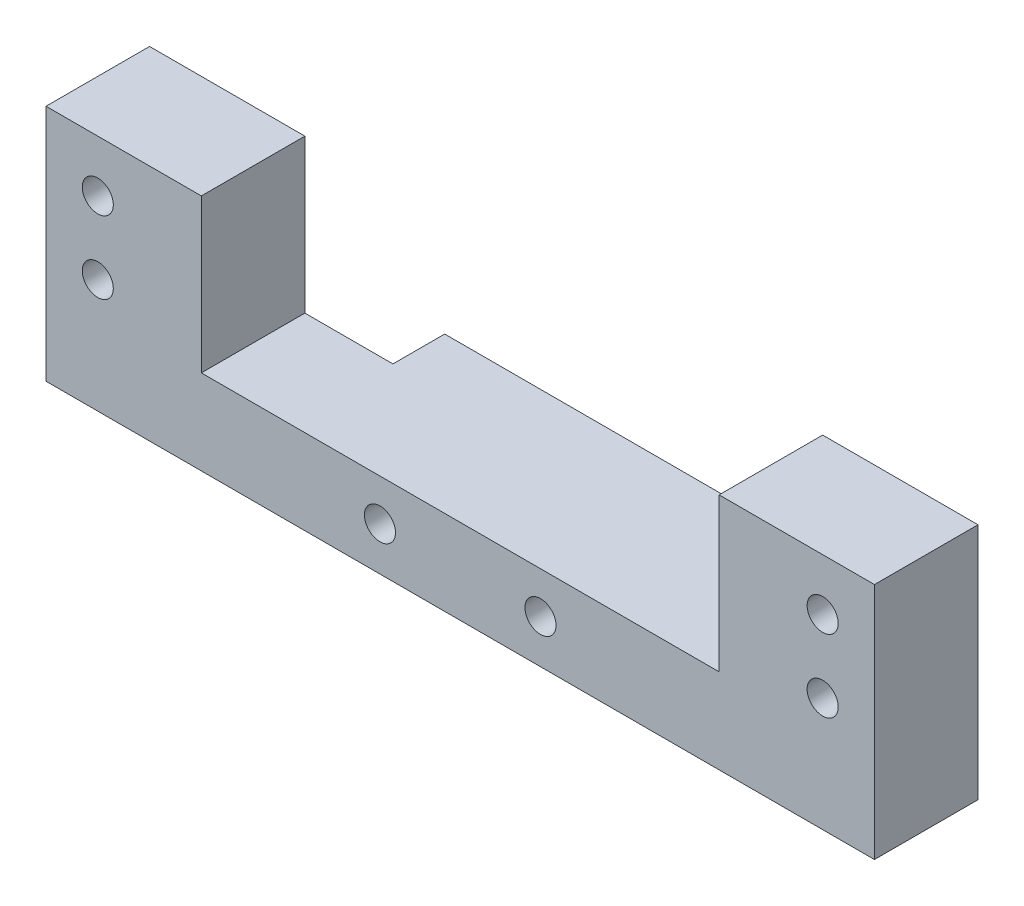
SolidWorks part; units mm, degrees
ref_plane "Front Plane" through (0, 0, 0) normal (0, 0, 1) x (1, 0, 0)
ref_plane "Top Plane" through (0, 0, 0) normal (0, 1, 0) x (1, 0, 0)
ref_plane "Right Plane" through (0, 0, 0) normal (1, 0, 0) x (0, 0, -1)
sketch "Sketch1" plane through (0, 0, 0) normal (0, 0, 1) x (1, 0, 0)
  line L1 (0, 0) -> (80, 0)
  line L2 (0, 0) -> (0, 23)
  line L3 (0, 23) -> (80, 23)
  line L4 (80, 0) -> (80, 23)
  dimension "D1" = 80
  dimension "D2" = 23
extrude "Boss-Extrude3" add sketch "Sketch1" along normal blind 10
sketch "Sketch4" plane through (0, 0, 10) normal (0, 0, 1) x (1, 0, 0)
  line L0 (80, 23) -> (0, 23) construction
  line L1 (15, 23) -> (65, 23)
  line L2 (15, 23) -> (15, 8.2)
  line L3 (15, 8.2) -> (65, 8.2)
  line L4 (65, 23) -> (65, 8.2)
  dimension "D1" = 15
  dimension "D2" = 15
  dimension "D3" = 8.2
extrude "Cut-Extrude1" cut sketch "Sketch4" against normal blind 10
sketch "Sketch6" plane through (0, 0, 10) normal (0, 0, 1) x (1, 0, 0)
  line L0 (40, 8.2) -> (40, 24.2609) construction
  line L1 (15, 8.2) -> (65, 8.2) construction
  line L2 (15, 23) -> (0, 23) construction
  line L4 (0, 23) -> (0, 0) construction
  circle A0 centre (5, 18) radius 1.5
  circle A1 centre (5, 11) radius 1.5
  circle A2 centre (75, 11) radius 1.5
  circle A3 centre (75, 18) radius 1.5
  dimension "D1" = 3
  dimension "D4" = 3
  dimension "D2" = 5
  dimension "D3" = 7
  dimension "D5" = 5
  dimension "D6" = 5
extrude "Cut-Extrude5" cut sketch "Sketch6" against normal blind 10
sketch "Sketch7" plane through (0, 0, 0) normal (0, 0, -1) x (-1, 0, 0)
  line L0 (-15, 8.2) -> (-65, 8.2) construction
  line L1 (-56.5, 8.2) -> (-23.5, 8.2)
  line L2 (-56.5, 8.2) -> (-56.5, 0)
  line L3 (-56.5, 0) -> (-23.5, 0)
  line L4 (-23.5, 8.2) -> (-23.5, 0)
  line L5 (0, 0) -> (-80, 0) construction
  dimension "D1" = 8.5
  dimension "D2" = 8.5
extrude "Boss-Extrude4" add sketch "Sketch7" along normal blind 5
sketch "Sketch5" plane through (0, 0, 10) normal (0, 0, 1) x (1, 0, 0)
  line L0 (40, 0) -> (40, 5.9954) construction
  line L1 (0, 0) -> (80, 0) construction
  line L2 (40, 5.9954) -> (27.75, 5.9954) construction
  line L3 (27.75, 5.9954) -> (27.75, 0) construction
  line L4 (15, 8.2) -> (65, 8.2) construction
  circle A0 centre (32.25, 4.2) radius 1.5
  circle A1 centre (47.75, 4.2) radius 1.5
  dimension "D2" = 3
  dimension "D1" = 12.25
  dimension "D3" = 4.5
  dimension "D4" = 4
extrude "Cut-Extrude2" cut sketch "Sketch5" against normal blind 19
